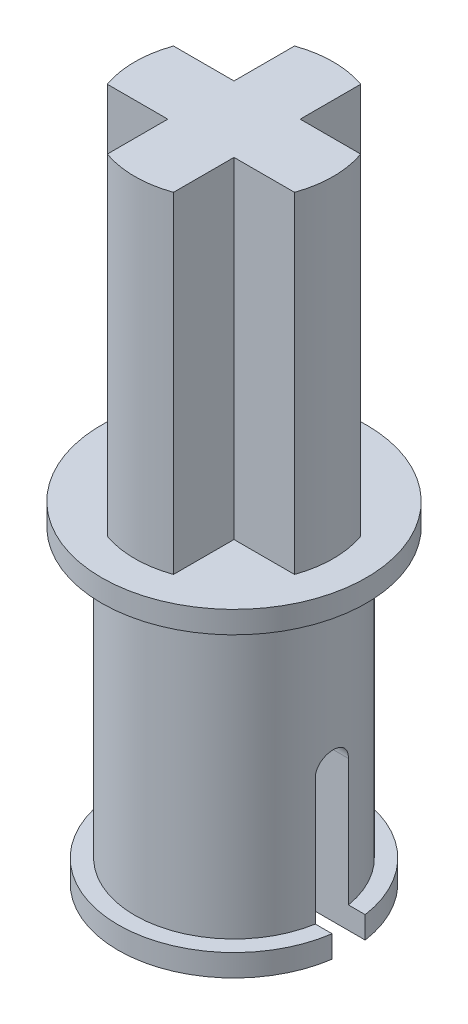
SolidWorks part; units mm, degrees
ref_plane "Front Plane" through (0, 0, 0) normal (0, 0, 1) x (1, 0, 0)
ref_plane "Top Plane" through (0, 0, 0) normal (0, 1, 0) x (1, 0, 0)
ref_plane "Right Plane" through (0, 0, 0) normal (1, 0, 0) x (0, 0, -1)
sketch "Sketch1" plane through (0, 0, 0) normal (0, 1, 0) x (1, 0, 0)
  circle A0 centre (0, 0) radius 1
  circle A1 centre (0, 0) radius 1.5
  dimension "D1" = 3
  dimension "D2" = 2
extrude "Boss-Extrude1" add sketch "Sketch1" along normal blind 5
sketch "Sketch2" plane through (0, 5, 0) normal (0, 1, 0) x (1, 0, 0)
  circle A0 centre (0, 0) radius 1
  circle A1 centre (0, 0) radius 2
  circle M1 centre (0, 0) radius 1.5
  circle M2 centre (0, 0) radius 1
  dimension "D1" = 4
extrude "Boss-Extrude2" add sketch "Sketch2" against normal blind 0.3333 contours M2 | A1 M1 | M1 M2
sketch "Sketch3" plane through (0, 0, 0) normal (0, -1, 0) x (-1, 0, 0)
  circle A0 centre (0, 0) radius 1.75
  circle A1 centre (0, 0) radius 1
  dimension "D1" = 3.5
extrude "Boss-Extrude4" add sketch "Sketch3" against normal blind 0.3333
sketch "Sketch4" plane through (0, 0, 0) normal (1, 0, 0) x (0, 0, -1)
  line L1 (0.25, 0) -> (-0.25, 0)
  line L2 (0.25, 0) -> (0.25, 2.25)
  line L3 (0.25, 2.25) -> (-0.25, 2.25)
  line L4 (-0.25, 0) -> (-0.25, 2.25)
  circle A0 centre (0, 2.25) radius 0.25
  point P7 (0, 0)
  dimension "D1" = 0.5
  dimension "D2" = 2.25
extrude "Cut-Extrude1" cut sketch "Sketch4" against normal through all both and the other way through all contours L3 A0
sketch "Sketch7" plane through (0, 5, 0) normal (0, 1, 0) x (1, 0, 0)
  line L1 (-0.5, 1.5) -> (0.5, 1.5)
  line L2 (-0.5, 1.5) -> (-0.5, -1.5)
  line L3 (-0.5, -1.5) -> (0.5, -1.5)
  line L4 (0.5, 1.5) -> (0.5, -1.5)
  line L5 (-0.5, 1.5) -> (0.5, -1.5) construction
  line L6 (-0.5, -1.5) -> (0.5, 1.5) construction
  line L7 (1.5, 0.5) -> (-1.5, 0.5)
  line L8 (1.5, 0.5) -> (1.5, -0.5)
  line L9 (1.5, -0.5) -> (-1.5, -0.5)
  line L10 (-1.5, 0.5) -> (-1.5, -0.5)
  line L11 (1.5, 0.5) -> (-1.5, -0.5) construction
  line L12 (1.5, -0.5) -> (-1.5, 0.5) construction
  circle A0 centre (0, 0) radius 1.5
  point P0 (0, 0)
  point P6 (0, 0)
  dimension "D1" = 1
  dimension "D2" = 3
  dimension "D3" = 3
  dimension "D4" = 1
extrude "Boss-Extrude6" add sketch "Sketch7" along normal blind 5 contours L9 A0 L7 L4 | L9 L4 L7 L2 | A0 L4 L9 L2 | L4 A0 L2 L7 | L7 A0 L9 L2
